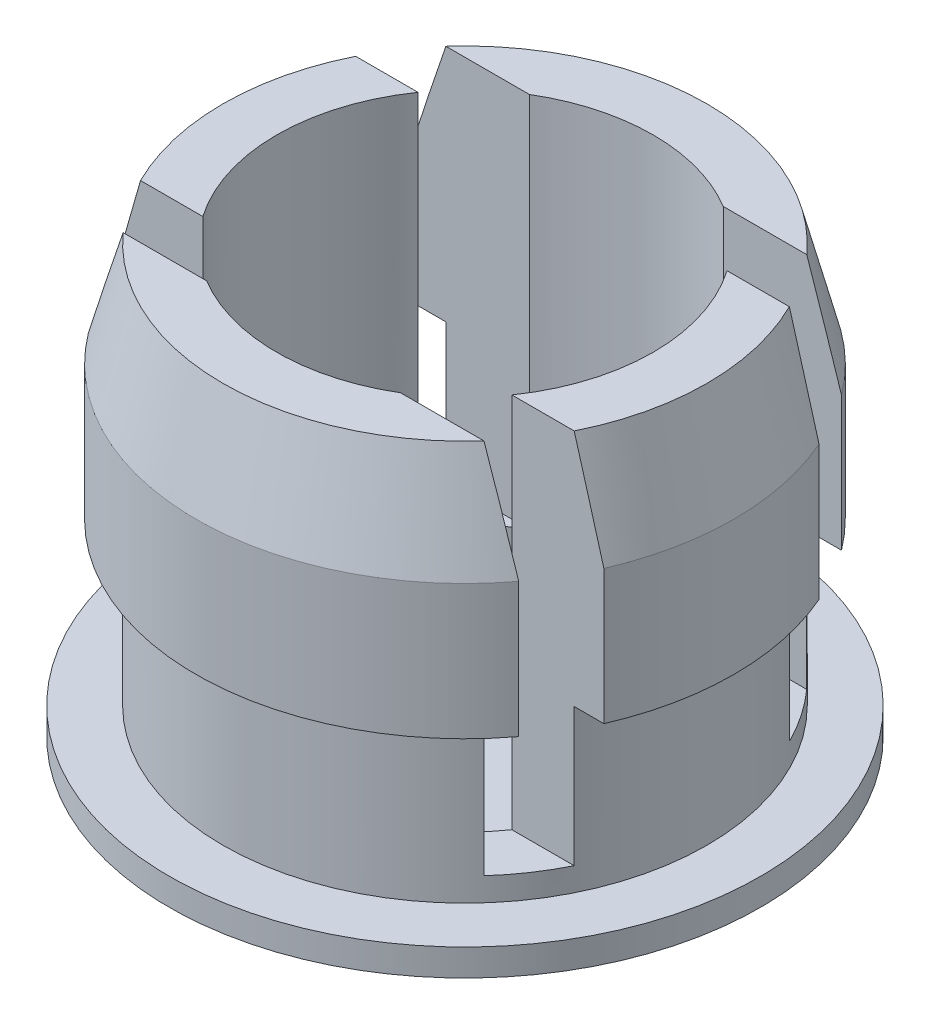
SolidWorks part; units mm, degrees
ref_plane "Alzado" through (0, 0, 0) normal (0, 0, 1) x (1, 0, 0)
ref_plane "Planta" through (0, 0, 0) normal (0, 1, 0) x (1, 0, 0)
ref_plane "Vista lateral" through (0, 0, 0) normal (1, 0, 0) x (0, 0, -1)
sketch "Croquis1" plane through (0, 0, 0) normal (0, 0, 1) x (1, 0, 0)
  line L1 (-89.7781, -14.638) -> (-78.7823, -14.638)
  line L2 (-78.7823, -14.638) -> (-78.7823, -13.638)
  line L3 (-87.7823, -13.638) -> (-87.7823, -7.638)
  line L4 (-87.7823, -7.638) -> (-88.7823, -7.638)
  line L5 (-88.7823, -7.638) -> (-88.7823, -2.638)
  line L6 (-88.7823, -2.638) -> (-87.7823, 1.236)
  line L7 (-87.7823, 1.236) -> (-85.7823, 1.236)
  line L8 (-85.7823, 1.236) -> (-85.7823, -13.638)
  line L9 (-85.7823, -13.638) -> (-78.7823, -13.638)
  line L11 (-89.7781, -13.638) -> (-89.7781, -14.638)
  line L14 (-87.7823, -13.638) -> (-89.7781, -13.638)
revolve "Revolución1" add sketch "Croquis1" angle 360 about L2
sketch "Croquis2" plane through (0, 1.236, 0) normal (0, 1, 0) x (1, 0, 0)
  line L0 (-87.7823, 0) -> (-69.7823, 0) construction
  line L6 (-91.7823, -4) -> (-65.7823, -4)
  line L7 (-91.7823, -4) -> (-91.7823, -6)
  line L8 (-91.7823, -6) -> (-65.7823, -6)
  line L9 (-65.7823, -4) -> (-65.7823, -6)
  line L10 (-91.7823, 4) -> (-65.7823, 4)
  line L11 (-91.7823, 4) -> (-91.7823, 6)
  line L12 (-91.7823, 6) -> (-65.7823, 6)
  line L13 (-65.7823, 4) -> (-65.7823, 6)
  circle A1 centre (-78.7823, 0) radius 9 construction
  dimension "D1" = 2
  dimension "D2" = 2
  dimension "D3" = 4
  dimension "D4" = 4
extrude "Cortar-Extruir1" cut sketch "Croquis2" against normal blind 14
